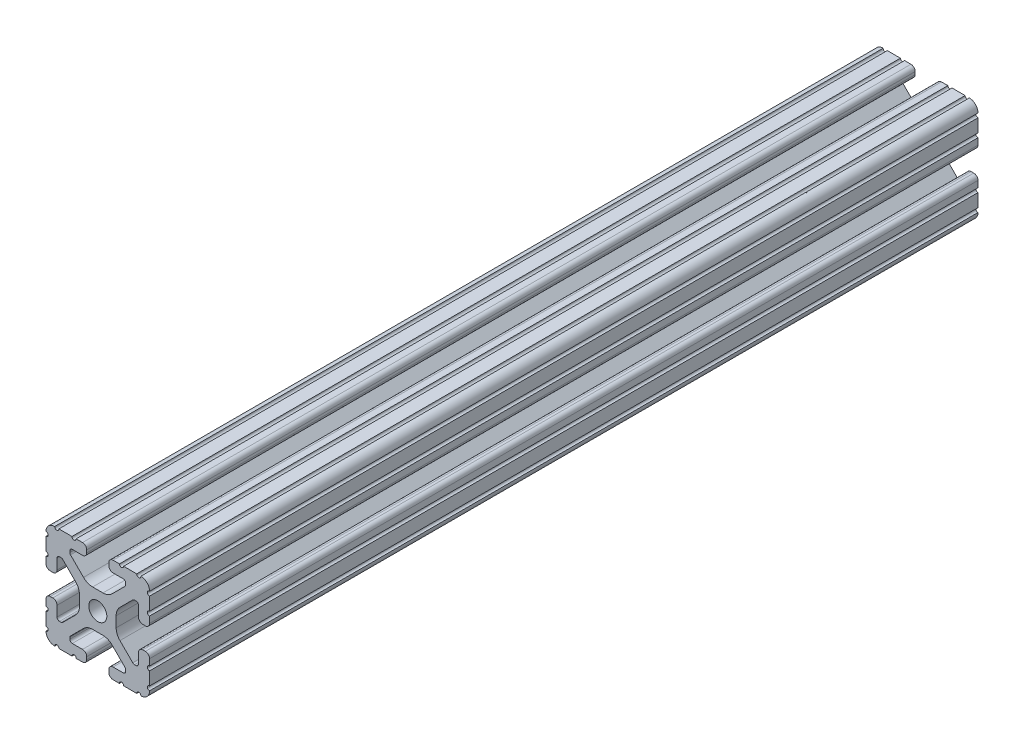
SolidWorks part; units mm, degrees
material "6061 Alloy"
ref_plane "Front Plane" through (0, 0, 0) normal (0, 0, 1) x (1, 0, 0)
ref_plane "Top Plane" through (0, 0, 0) normal (0, 1, 0) x (1, 0, 0)
ref_plane "Right Plane" through (0, 0, 0) normal (1, 0, 0) x (0, 0, -1)
sketch "Sketch1" plane through (0, 0, 0) normal (0, 0, 1) x (1, 0, 0)
  line L0 (0, 25.6181) -> (0, -24.623) construction
  line L1 (-20.8943, 0) -> (20.4607, 0) construction
  line L2 (-10.0229, 12.9148) -> (-5.2522, 8.144)
  line L3 (-10.287, 14.0843) -> (-10.287, 13.5524)
  line L4 (-5.6176, 14.986) -> (-9.3853, 14.986)
  line L5 (-4.064, 17.4964) -> (-4.064, 16.5396)
  line L6 (-7.9742, 19.05) -> (-5.6176, 19.05)
  line L7 (-14.3277, 19.05) -> (-9.4982, 19.05)
  line L8 (-19.05, 9.4961) -> (-19.05, 14.3277)
  line L9 (-19.05, 5.6176) -> (-19.05, 7.9763)
  line L10 (-16.5396, 4.064) -> (-17.4964, 4.064)
  line L11 (-14.986, 9.3853) -> (-14.986, 5.6176)
  line L12 (-13.516, 10.287) -> (-14.0843, 10.287)
  line L13 (-8.1476, 5.2921) -> (-12.8784, 10.0229)
  line L14 (-6.7564, -1.9335) -> (-6.7564, 1.9335)
  line L15 (-12.8784, -10.0229) -> (-8.1476, -5.2921)
  line L16 (-14.0843, -10.287) -> (-13.516, -10.287)
  line L17 (-14.986, -5.6176) -> (-14.986, -9.3853)
  line L18 (-17.4964, -4.064) -> (-16.5396, -4.064)
  line L19 (-19.05, -7.9763) -> (-19.05, -5.6176)
  line L20 (-19.05, -14.3277) -> (-19.05, -9.4961)
  line L21 (-9.4961, -19.05) -> (-14.3277, -19.05)
  line L22 (-5.6176, -19.05) -> (-7.9763, -19.05)
  line L23 (-4.064, -17.4964) -> (-4.064, -16.5396)
  line L24 (10.0229, -12.9148) -> (5.2522, -8.144)
  line L25 (10.287, -14.0843) -> (10.287, -13.5524)
  line L26 (5.6176, -14.986) -> (9.3853, -14.986)
  line L28 (-1.9022, 6.7564) -> (1.9022, 6.7564)
  line L29 (-1.9022, -6.7564) -> (1.9022, -6.7564)
  line L31 (-5.6176, -14.986) -> (-9.3853, -14.986)
  line L32 (-10.287, -14.0843) -> (-10.287, -13.5524)
  line L33 (-10.0229, -12.9148) -> (-5.2522, -8.144)
  line L66 (4.064, -16.5396) -> (4.064, -17.4964)
  line L67 (5.6176, -19.05) -> (7.9763, -19.05)
  line L68 (9.4961, -19.05) -> (14.3277, -19.05)
  line L69 (19.05, -14.3277) -> (19.05, -9.4961)
  line L70 (19.05, -7.9763) -> (19.05, -5.6176)
  line L71 (17.4964, -4.064) -> (16.5396, -4.064)
  line L72 (14.986, -5.6176) -> (14.986, -9.3853)
  line L73 (14.0843, -10.287) -> (13.516, -10.287)
  line L74 (12.8784, -10.0229) -> (8.1476, -5.2921)
  line L75 (6.7564, -1.9335) -> (6.7564, 1.9335)
  line L76 (8.1476, 5.2921) -> (12.8784, 10.0229)
  line L77 (13.516, 10.287) -> (14.0843, 10.287)
  line L78 (14.986, 9.3853) -> (14.986, 5.6176)
  line L79 (16.5396, 4.064) -> (17.4964, 4.064)
  line L80 (19.05, 5.6176) -> (19.05, 7.9763)
  line L81 (19.05, 9.4961) -> (19.05, 14.3277)
  line L82 (14.3277, 19.05) -> (9.4982, 19.05)
  line L83 (7.9742, 19.05) -> (5.6176, 19.05)
  line L84 (4.064, 17.4964) -> (4.064, 16.5396)
  line L85 (5.6176, 14.986) -> (9.3853, 14.986)
  line L86 (10.287, 14.0843) -> (10.287, 13.5524)
  line L87 (10.0229, 12.9148) -> (5.2522, 8.144)
  arc A0 (-10.0229, 12.9148) -> (-10.287, 13.5524) centre (-9.3853, 13.5524) cw
  circle A1 centre (0, 0) radius 3.3274
  arc A2 (-10.287, 14.0843) -> (-9.3853, 14.986) centre (-9.3853, 14.0843) cw
  arc A3 (-4.064, 16.5396) -> (-5.6176, 14.986) centre (-5.6176, 16.5396) cw
  arc A4 (-5.6176, 19.05) -> (-4.064, 17.4964) centre (-5.6176, 17.4964) cw
  arc A5 (-7.9742, 19.05) -> (-9.4982, 19.05) centre (-8.7362, 19.05) cw
  arc A6 (-14.3277, 19.05) -> (-15.8475, 19.05) centre (-15.0876, 18.9933) cw
  arc A7 (-19.05, 15.8475) -> (-15.8475, 19.05) centre (-15.8751, 15.8751) cw
  arc A8 (-19.05, 15.8475) -> (-19.05, 14.3277) centre (-18.9933, 15.0876) cw
  arc A9 (-19.05, 9.4961) -> (-19.05, 7.9763) centre (-18.9933, 8.7362) cw
  arc A10 (-17.4964, 4.064) -> (-19.05, 5.6176) centre (-17.4964, 5.6176) cw
  arc A11 (-14.986, 5.6176) -> (-16.5396, 4.064) centre (-16.5396, 5.6176) cw
  arc A12 (-14.986, 9.3853) -> (-14.0843, 10.287) centre (-14.0843, 9.3853) cw
  arc A13 (-13.516, 10.287) -> (-12.8784, 10.0229) centre (-13.516, 9.3853) cw
  arc A14 (-8.1476, 5.2921) -> (-6.7564, 1.9335) centre (-11.5062, 1.9335) cw
  arc A15 (-6.7564, -1.9335) -> (-8.1476, -5.2921) centre (-11.5062, -1.9335) cw
  arc A16 (-12.8784, -10.0229) -> (-13.516, -10.287) centre (-13.516, -9.3853) cw
  arc A17 (-14.0843, -10.287) -> (-14.986, -9.3853) centre (-14.0843, -9.3853) cw
  arc A18 (-16.5396, -4.064) -> (-14.986, -5.6176) centre (-16.5396, -5.6176) cw
  arc A19 (-19.05, -5.6176) -> (-17.4964, -4.064) centre (-17.4964, -5.6176) cw
  arc A20 (-19.05, -7.9763) -> (-19.05, -9.4961) centre (-18.9933, -8.7362) cw
  arc A21 (-19.05, -14.3277) -> (-19.05, -15.8475) centre (-18.9933, -15.0876) cw
  arc A22 (-15.8475, -19.05) -> (-19.05, -15.8475) centre (-15.8751, -15.8751) cw
  arc A23 (-15.8475, -19.05) -> (-14.3277, -19.05) centre (-15.0876, -18.9933) cw
  arc A24 (-9.4961, -19.05) -> (-7.9763, -19.05) centre (-8.7362, -18.9933) cw
  arc A25 (-4.064, -17.4964) -> (-5.6176, -19.05) centre (-5.6176, -17.4964) cw
  arc A26 (-5.2522, -8.144) -> (-1.9022, -6.7564) centre (-1.9022, -11.494) cw
  arc A27 (1.9022, -6.7564) -> (5.2522, -8.144) centre (1.9022, -11.494) cw
  arc A28 (10.0229, -12.9148) -> (10.287, -13.5524) centre (9.3853, -13.5524) cw
  arc A29 (10.287, -14.0843) -> (9.3853, -14.986) centre (9.3853, -14.0843) cw
  arc A30 (4.064, -16.5396) -> (5.6176, -14.986) centre (5.6176, -16.5396) cw
  arc A31 (-4.064, -16.5396) -> (-5.6176, -14.986) centre (-5.6176, -16.5396) ccw
  arc A32 (-10.287, -14.0843) -> (-9.3853, -14.986) centre (-9.3853, -14.0843) ccw
  arc A33 (-10.0229, -12.9148) -> (-10.287, -13.5524) centre (-9.3853, -13.5524) ccw
  arc A79 (4.064, -17.4964) -> (5.6176, -19.05) centre (5.6176, -17.4964) ccw
  arc A80 (9.4961, -19.05) -> (7.9763, -19.05) centre (8.7362, -18.9933) ccw
  arc A81 (15.8475, -19.05) -> (14.3277, -19.05) centre (15.0876, -18.9933) ccw
  arc A82 (15.8475, -19.05) -> (19.05, -15.8475) centre (15.8751, -15.8751) ccw
  arc A83 (19.05, -14.3277) -> (19.05, -15.8475) centre (18.9933, -15.0876) ccw
  arc A84 (19.05, -7.9763) -> (19.05, -9.4961) centre (18.9933, -8.7362) ccw
  arc A85 (19.05, -5.6176) -> (17.4964, -4.064) centre (17.4964, -5.6176) ccw
  arc A86 (16.5396, -4.064) -> (14.986, -5.6176) centre (16.5396, -5.6176) ccw
  arc A87 (14.0843, -10.287) -> (14.986, -9.3853) centre (14.0843, -9.3853) ccw
  arc A88 (12.8784, -10.0229) -> (13.516, -10.287) centre (13.516, -9.3853) ccw
  arc A89 (6.7564, -1.9335) -> (8.1476, -5.2921) centre (11.5062, -1.9335) ccw
  arc A90 (8.1476, 5.2921) -> (6.7564, 1.9335) centre (11.5062, 1.9335) ccw
  arc A91 (13.516, 10.287) -> (12.8784, 10.0229) centre (13.516, 9.3853) ccw
  arc A92 (14.986, 9.3853) -> (14.0843, 10.287) centre (14.0843, 9.3853) ccw
  arc A93 (14.986, 5.6176) -> (16.5396, 4.064) centre (16.5396, 5.6176) ccw
  arc A94 (17.4964, 4.064) -> (19.05, 5.6176) centre (17.4964, 5.6176) ccw
  arc A95 (19.05, 9.4961) -> (19.05, 7.9763) centre (18.9933, 8.7362) ccw
  arc A96 (19.05, 15.8475) -> (19.05, 14.3277) centre (18.9933, 15.0876) ccw
  arc A97 (19.05, 15.8475) -> (15.8475, 19.05) centre (15.8751, 15.8751) ccw
  arc A98 (14.3277, 19.05) -> (15.8475, 19.05) centre (15.0876, 18.9933) ccw
  arc A99 (7.9742, 19.05) -> (9.4982, 19.05) centre (8.7362, 19.05) ccw
  arc A100 (5.6176, 19.05) -> (4.064, 17.4964) centre (5.6176, 17.4964) ccw
  arc A101 (4.064, 16.5396) -> (5.6176, 14.986) centre (5.6176, 16.5396) ccw
  arc A102 (10.287, 14.0843) -> (9.3853, 14.986) centre (9.3853, 14.0843) ccw
  arc A103 (10.0229, 12.9148) -> (10.287, 13.5524) centre (9.3853, 13.5524) ccw
  arc A104 (1.9022, 6.7564) -> (5.2522, 8.144) centre (1.9022, 11.494) ccw
  arc A105 (-5.2522, 8.144) -> (-1.9022, 6.7564) centre (-1.9022, 11.494) ccw
  dimension "D1" = 6.6548
  dimension "D2" = 19.05
  dimension "D3" = 38.1
  dimension "D4" = 20.574
  dimension "D5" = 13.5128
  dimension "D6" = 4.064
  dimension "D7" = 8.128
  dimension "D8" = 4.064
  dimension "D9" = 12.2936
extrude "Extrude1" add sketch "Sketch1" against normal blind 304.8
